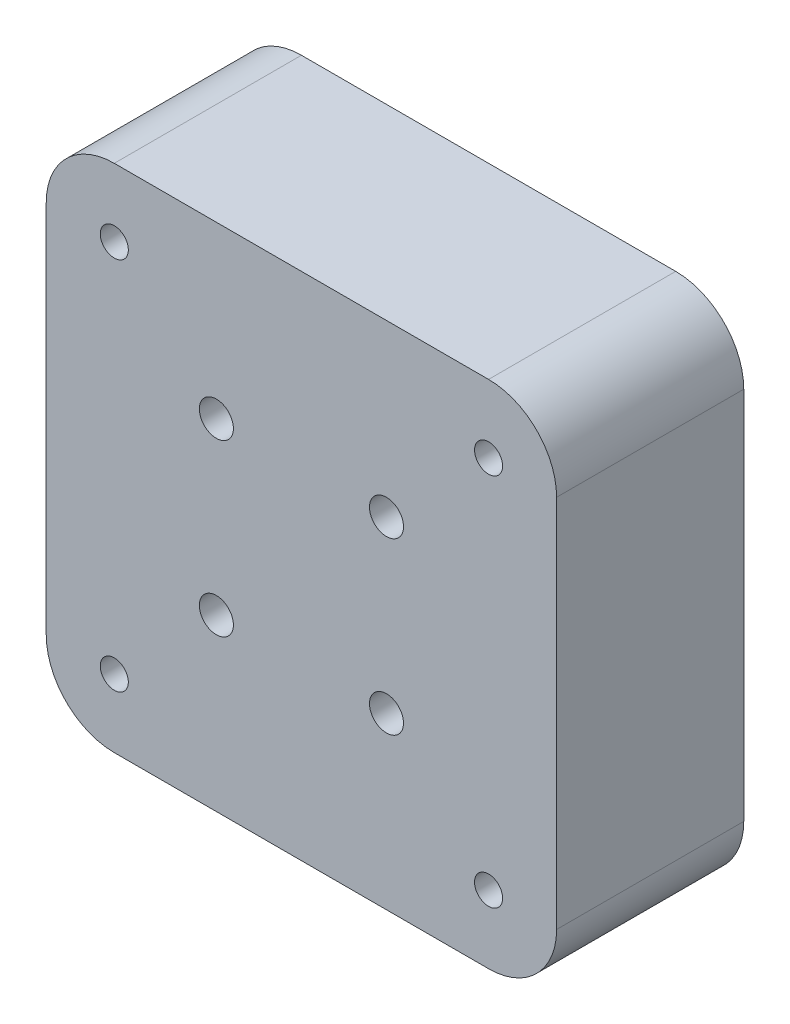
SolidWorks part; units mm, degrees
ref_plane "Front" through (0, 0, 0) normal (0, 0, 1) x (1, 0, 0)
ref_plane "Top" through (0, 0, 0) normal (0, 1, 0) x (1, 0, 0)
ref_plane "Right" through (0, 0, 0) normal (1, 0, 0) x (0, 0, -1)
sketch "Sketch1" plane through (0, 0, 0) normal (0, 0, 1) x (1, 0, 0)
  line L1 (-30, 30) -> (30, 30)
  line L2 (-30, 30) -> (-30, -30)
  line L3 (-30, -30) -> (30, -30)
  line L4 (30, 30) -> (30, -30)
  line L5 (0, -30) -> (0, 30) construction
  line L6 (-30, 0) -> (30, 0) construction
  point P0 (0, 0)
  dimension "D1" = 60
  dimension "D2" = 60
extrude "Boss-Extrude1" add sketch "Sketch1" along normal blind 22
fillet "Fillet1" radius 8 4 edges at (30, -30, 11) (-30, -30, 11) (30, 30, 11) (-30, 30, 11)
hole_wizard "M4x0.7 Tapped Hole1" positions "Sketch4" profile "Sketch3" tap size "M4x0.7" standard "ANSI Metric" end condition through all
sketch "Sketch4" plane through (0, 0, 0) normal (0, 0, -1) x (-1, 0, 0)
  point P0 (-22, 22)
  point P2 (22, 22)
  point P4 (22, -22)
  point P6 (-22, -22)
  dimension "D1" = 22
  dimension "D2" = 22
  dimension "D3" = 22
  dimension "D4" = 22
sketch "Sketch3" plane through (22, 22, 0) normal (1, 0, 0) x (0, 1, 0)
  line L0 (0, 0) -> (0, 22)
  line L1 (0, 22) -> (1.65, 22)
  line L2 (1.65, 22) -> (1.65, 0)
  line L5 (1.65, 0) -> (0, 0)
  line L11 (0, -6.35) -> (0, 107.95) construction
  dimension "Thru Tap Drill Dia." = 3.3
  dimension "Thru Tap Drill Depth" = 22
cosmetic thread "Hole Thread1" parameters "D2"=4
cosmetic thread "Hole Thread2" parameters "D2"=4
cosmetic thread "Hole Thread3" parameters "D2"=4
cosmetic thread "Hole Thread4" parameters "D2"=4
sketch "Sketch5" plane through (0, 0, 0) normal (0, 0, -1) x (-1, 0, 0)
  line L1 (-15, 20) -> (15, 20)
  line L2 (-20, 15) -> (-20, -15)
  line L3 (-15, -20) -> (15, -20)
  line L4 (20, 15) -> (20, -15)
  line L7 (-20, 0) -> (0, 0) construction
  line L8 (0, 0) -> (0, 20) construction
  arc A0 (-20, -15) -> (-15, -20) centre (-15, -15) ccw
  arc A1 (15, -20) -> (20, -15) centre (15, -15) ccw
  arc A2 (20, 15) -> (15, 20) centre (15, 15) ccw
  arc A3 (-15, 20) -> (-20, 15) centre (-15, 15) ccw
  point P13 (20, 20)
  point P16 (-20, 20)
  dimension "D1" = 40
  dimension "D2" = 5
extrude "Cut-Extrude1" cut sketch "Sketch5" against normal blind 10
sketch "Sketch6" plane through (0, 0, 22) normal (0, 0, 1) x (1, 0, 0)
  circle A0 centre (-10, 10) radius 2
  circle A1 centre (10, 10) radius 2
  circle A2 centre (10, -10) radius 2
  circle A3 centre (-10, -10) radius 2
  dimension "D1" = 20
  dimension "D2" = 10
  dimension "D3" = 20
  dimension "D4" = 10
  dimension "D5" = 4
extrude "Cut-Extrude2" cut sketch "Sketch6" against normal through all
